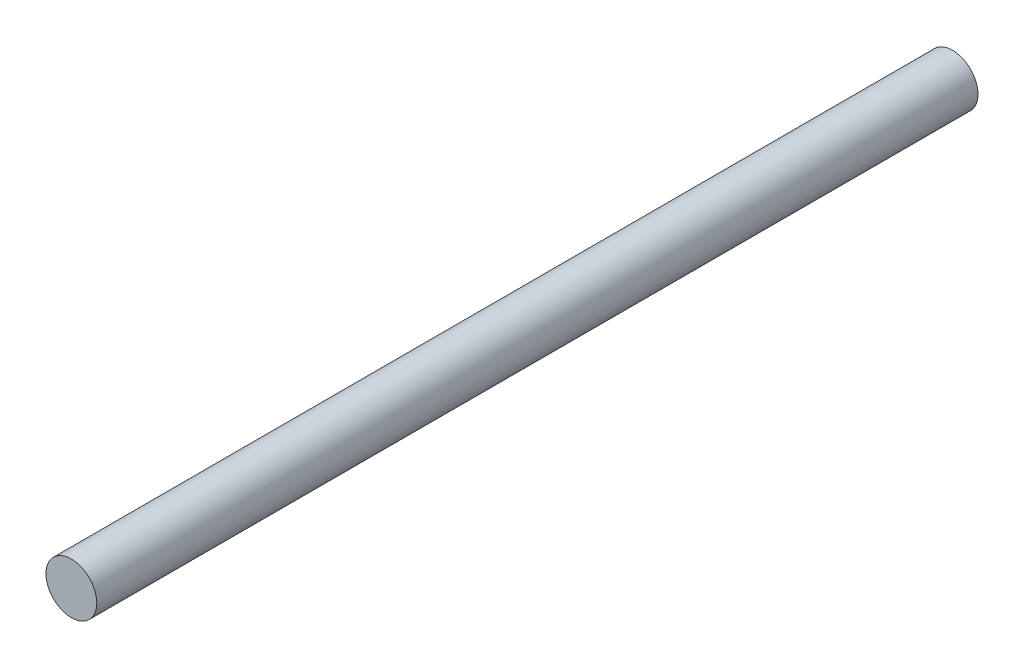
SolidWorks part; units mm, degrees
ref_plane "Front Plane" through (0, 0, 0) normal (0, 0, 1) x (1, 0, 0)
ref_plane "Top Plane" through (0, 0, 0) normal (0, 1, 0) x (1, 0, 0)
ref_plane "Right Plane" through (0, 0, 0) normal (1, 0, 0) x (0, 0, -1)
sketch "Sketch1" plane through (0, 0, 0) normal (0, 0, 1) x (1, 0, 0)
  circle A0 centre (0, 0) radius 19.05
  dimension "D1" = 38.1
extrude "Boss-Extrude1" add sketch "Sketch1" along normal mid plane 660.4
